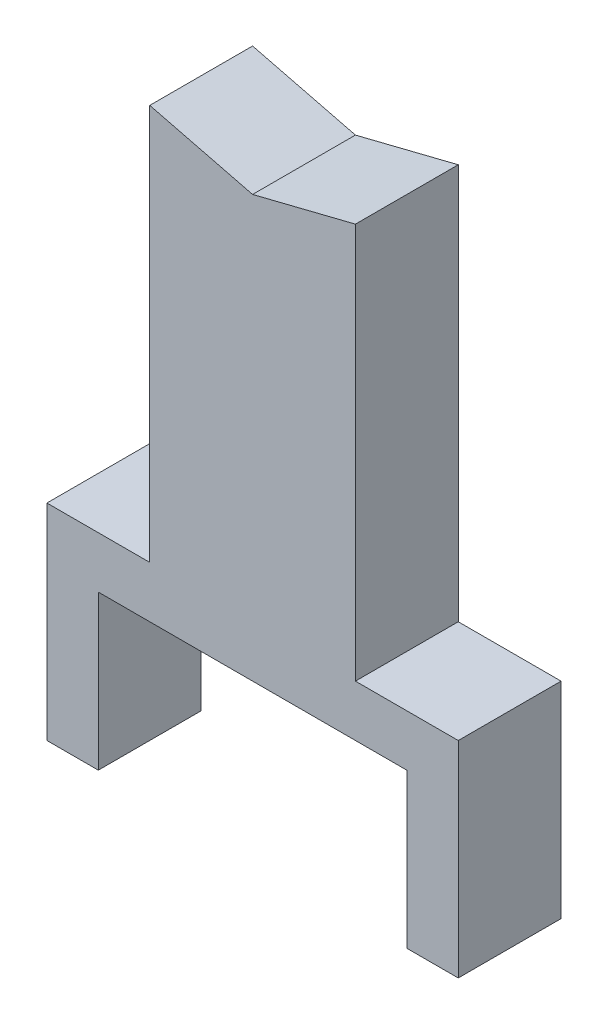
SolidWorks part; units mm, degrees
ref_plane "Front Plane" through (0, 0, 0) normal (0, 0, 1) x (1, 0, 0)
ref_plane "Top Plane" through (0, 0, 0) normal (0, 1, 0) x (1, 0, 0)
ref_plane "Right Plane" through (0, 0, 0) normal (1, 0, 0) x (0, 0, -1)
sketch "Sketch1" plane through (0, 0, 0) normal (0, 0, 1) x (1, 0, 0)
  line L0 (-50.8, 297.1038) -> (0, 284.4038)
  line L2 (-50.8, 101.6) -> (-50.8, 297.1038)
  line L4 (50.8, 101.6) -> (50.8, 297.1038)
  line L5 (0, 284.4038) -> (50.8, 297.1038)
  line L6 (0, 284.4038) -> (0, 0) construction
  line L11 (-76.2, 0) -> (-76.2, 76.2)
  line L12 (-76.2, 76.2) -> (0, 76.2)
  line L13 (-76.2, 0) -> (-101.6, 0)
  line L14 (-101.6, 0) -> (-101.6, 101.6)
  line L15 (-101.6, 101.6) -> (-50.8, 101.6)
  line L17 (101.6, 101.6) -> (50.8, 101.6)
  line L18 (101.6, 0) -> (101.6, 101.6)
  line L19 (76.2, 0) -> (101.6, 0)
  line L20 (76.2, 0) -> (76.2, 76.2)
  line L21 (76.2, 76.2) -> (0, 76.2)
  point P0 (-76.2, 38.1)
  dimension "D1" = 203.2
  dimension "D2" = 101.6
  dimension "D3" = 12.7
  dimension "D4" = 101.6
  dimension "D5" = 25.4
  dimension "D6" = 25.4
  dimension "D7" = 297.1038
extrude "Boss-Extrude1" add sketch "Sketch1" along normal mid plane 50.8
